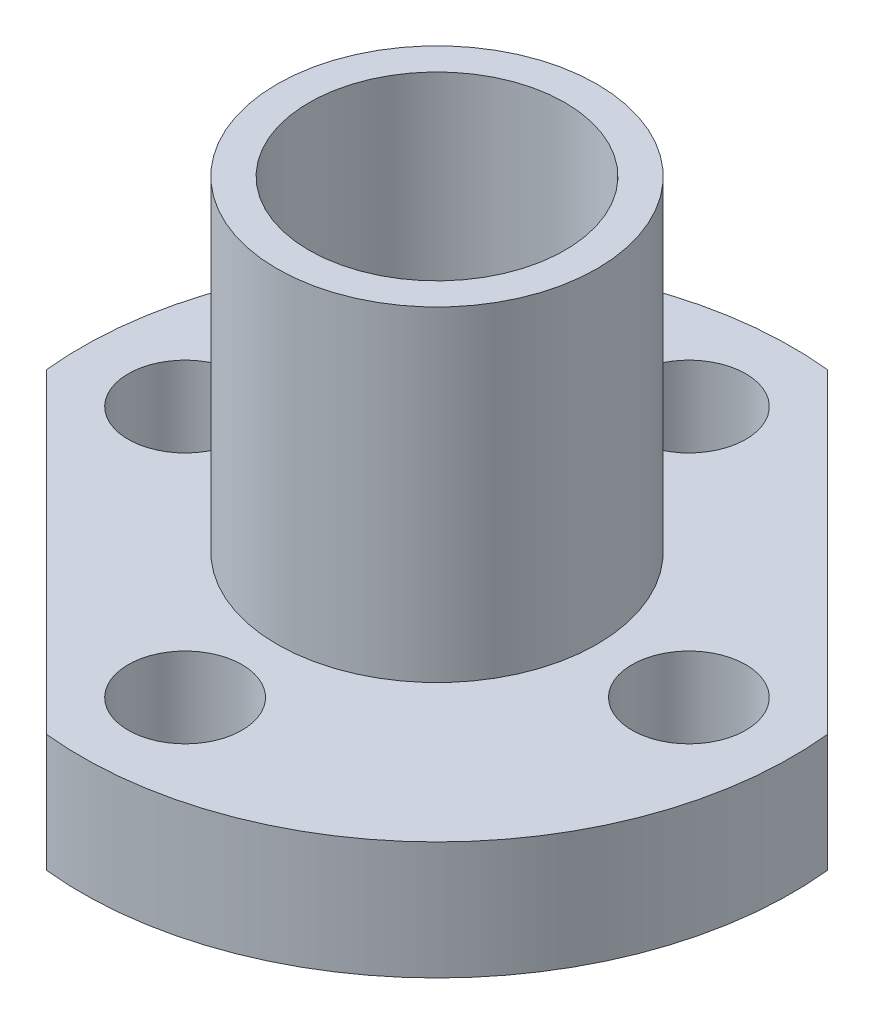
SolidWorks part; units mm, degrees
ref_plane "Front Plane" through (0, 0, 0) normal (0, 0, 1) x (1, 0, 0)
ref_plane "Top Plane" through (0, 0, 0) normal (0, 1, 0) x (1, 0, 0)
ref_plane "Right Plane" through (0, 0, 0) normal (1, 0, 0) x (0, 0, -1)
sketch "Sketch1" plane through (0, 0, 0) normal (0, 1, 0) x (1, 0, 0)
  circle A0 centre (0, 0) radius 4
  circle A1 centre (0, 0) radius 5
extrude "Boss-Extrude1" add sketch "Sketch1" along normal blind 15.6
ref_plane "Plane1" through (0, 1.75, 0) normal (0, -1, 0) x (-1, 0, 0)
sketch "Sketch2" plane through (0, 1.75, 0) normal (0, -1, 0) x (-1, 0, 0)
  circle A0 centre (0, 0) radius 11.1
  circle A1 centre (0, 0) radius 5 construction
  circle A2 centre (0, 0) radius 5
  circle A3 centre (0, 7.874) radius 1.778
  circle A4 centre (0, 0) radius 7.874 construction
  circle A5 centre (7.874, 0) radius 1.778
  circle A6 centre (0, -7.874) radius 1.778
  circle A7 centre (-7.874, 0) radius 1.778
  point P2 (0, 6.096)
  point P14 (0, 5)
  dimension "D1" = 15.748
  dimension "D2" = 3.556
extrude "Boss-Extrude2" add sketch "Sketch2" against normal blind 3.683
sketch "Sketch3" plane through (0, 1.75, 0) normal (0, -1, 0) x (1, 0, 0)
  line L0 (0.0109, -12.2023) -> (16.3166, 4.1035)
  line L1 (16.3166, 4.1035) -> (4.1035, 16.3166)
  line L2 (4.1035, 16.3166) -> (-15.6061, -3.3929)
  line L3 (-15.6061, -3.3929) -> (-3.3929, -15.6061)
  line L4 (-3.3929, -15.6061) -> (0.0109, -12.2023)
  dimension "D1" = 8.636
  dimension "D2" = 8.636
extrude "Cut-Extrude1" cut sketch "Sketch3" against normal through all flip side to cut
